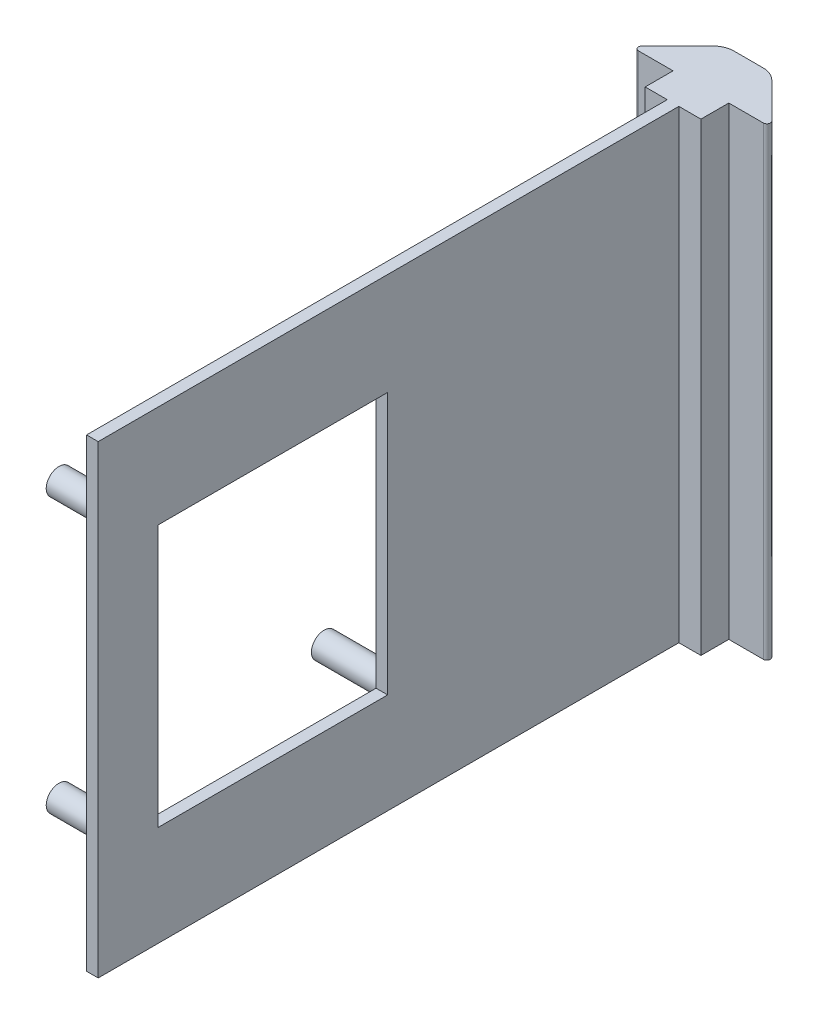
SolidWorks part; units mm, degrees
ref_plane "Front Plane" through (0, 0, 0) normal (0, 0, 1) x (1, 0, 0)
ref_plane "Top Plane" through (0, 0, 0) normal (0, 1, 0) x (1, 0, 0)
ref_plane "Right Plane" through (0, 0, 0) normal (1, 0, 0) x (0, 0, -1)
sketch "Sketch1" plane through (0, 273.1831, 0) normal (0, 1, 0) x (1, 0, 0)
  line L42 (-29.6676, -22.3423) -> (-29.6676, -22.5963)
  line L43 (-29.6676, -22.5963) -> (-27.2546, -22.5963)
  line L44 (-27.2546, -22.5963) -> (-27.2546, -86.0963)
  line L45 (-27.2546, -86.0963) -> (-25.9846, -86.0963)
  line L46 (-23.5716, -19.5483) -> (-23.5716, -22.3423)
  line L47 (-29.6676, -22.3423) -> (-29.6676, -19.5483)
  line L48 (-29.6676, -19.5483) -> (-33.4506, -19.5483)
  line L49 (-19.7887, -19.5483) -> (-23.5716, -19.5483)
  line L50 (-23.4064, -15.0109) -> (-19.5193, -18.8979)
  line L51 (-28.2165, -14.3413) -> (-25.0228, -14.3413)
  line L52 (-33.72, -18.8979) -> (-29.8329, -15.0109)
  line L53 (-23.5716, -19.5483) -> (-23.5716, -22.3423)
  line L54 (-29.6676, -22.3423) -> (-29.6676, -19.5483)
  line L55 (-29.6676, -19.5483) -> (-33.4506, -19.5483)
  line L56 (-19.7887, -19.5483) -> (-23.5716, -19.5483)
  line L57 (-23.4064, -15.0109) -> (-19.5193, -18.8979)
  line L58 (-28.2165, -14.3413) -> (-25.0228, -14.3413)
  line L59 (-33.72, -18.8979) -> (-29.8329, -15.0109)
  line L60 (-25.9846, -86.0963) -> (-25.9846, -22.5963)
  line L61 (-25.9846, -22.5963) -> (-23.5716, -22.5963)
  line L62 (-23.5716, -22.5963) -> (-23.5716, -22.3423)
  arc A31 (-33.72, -18.8979) -> (-33.4506, -19.5483) centre (-33.4506, -19.1673) ccw
  arc A32 (-19.7887, -19.5483) -> (-19.5193, -18.8979) centre (-19.7887, -19.1673) ccw
  arc A33 (-23.4064, -15.0109) -> (-25.0228, -14.3413) centre (-25.0228, -16.6273) ccw
  arc A34 (-28.2165, -14.3413) -> (-29.8329, -15.0109) centre (-28.2165, -16.6273) ccw
  arc A35 (-33.72, -18.8979) -> (-33.4506, -19.5483) centre (-33.4506, -19.1673) ccw
  arc A36 (-19.7887, -19.5483) -> (-19.5193, -18.8979) centre (-19.7887, -19.1673) ccw
  arc A37 (-23.4064, -15.0109) -> (-25.0228, -14.3413) centre (-25.0228, -16.6273) ccw
  arc A38 (-28.2165, -14.3413) -> (-29.8329, -15.0109) centre (-28.2165, -16.6273) ccw
  point P6 (-24.0796, -22.492)
  dimension "D2" = 1.27
  dimension "D3" = 63.5
  dimension "D4" = 0.254
  dimension "D5" = 0.254
  dimension "D1" = 0.254
extrude "Boss-Extrude1" add sketch "Sketch1" against normal blind 50.8
sketch "Sketch2" plane through (-27.2546, 0, 0) normal (-1, 0, 0) x (0, 0, 1)
  line L8 (88.6363, 275.7231) -> (20.0563, 275.7231)
  line L9 (20.0563, 275.7231) -> (20.0563, 219.8431)
  line L10 (20.0563, 219.8431) -> (88.6363, 219.8431)
  line L11 (88.6363, 219.8431) -> (88.6363, 275.7231)
  line L12 (88.6363, 275.7231) -> (20.0563, 275.7231)
  line L13 (20.0563, 275.7231) -> (20.0563, 219.8431)
  line L14 (20.0563, 219.8431) -> (88.6363, 219.8431)
  line L15 (88.6363, 219.8431) -> (88.6363, 275.7231)
  circle A0 centre (81.4947, 262.6903) radius 1.397
  circle A1 centre (81.4947, 232.6903) radius 1.397
  circle A2 centre (52.4947, 232.6903) radius 1.397
  circle A3 centre (52.4947, 262.6903) radius 1.397
  dimension "D2" = 2.794
  dimension "D1" = 2.54
extrude "Boss-Extrude3" add sketch "Sketch2" along normal blind 7.62 contours A2 | A3 | A0 | A1
sketch "Sketch4" plane through (-27.2546, 0, 0) normal (-1, 0, 0) x (0, 0, 1)
  line L0 (83.9947, 265.1903) -> (83.9947, 230.1903) construction
  line L1 (83.9947, 230.1903) -> (49.9947, 230.1903) construction
  line L2 (49.9947, 265.1903) -> (83.9947, 265.1903) construction
  line L8 (88.6363, 275.7231) -> (20.0563, 275.7231)
  line L9 (20.0563, 275.7231) -> (20.0563, 219.8431)
  line L10 (20.0563, 219.8431) -> (88.6363, 219.8431)
  line L11 (88.6363, 219.8431) -> (88.6363, 275.7231)
  line L12 (88.6363, 275.7231) -> (20.0563, 275.7231)
  line L13 (20.0563, 275.7231) -> (20.0563, 219.8431)
  line L14 (20.0563, 219.8431) -> (88.6363, 219.8431)
  line L15 (88.6363, 219.8431) -> (88.6363, 275.7231)
  line L16 (49.9947, 230.1903) -> (49.9947, 265.1903) construction
  line L17 (54.4397, 262.0153) -> (79.5497, 262.0153)
  line L18 (54.4397, 262.0153) -> (54.4397, 233.3653)
  line L19 (54.4397, 233.3653) -> (79.5497, 233.3653)
  line L20 (79.5497, 262.0153) -> (79.5497, 233.3653)
  dimension "D2" = 4.445
  dimension "D3" = 4.445
  dimension "D4" = 3.175
  dimension "D5" = 3.175
  dimension "D1" = 2.54
extrude "Cut-Extrude2" cut sketch "Sketch4" against normal through all contours L20 L17 L18 L19
